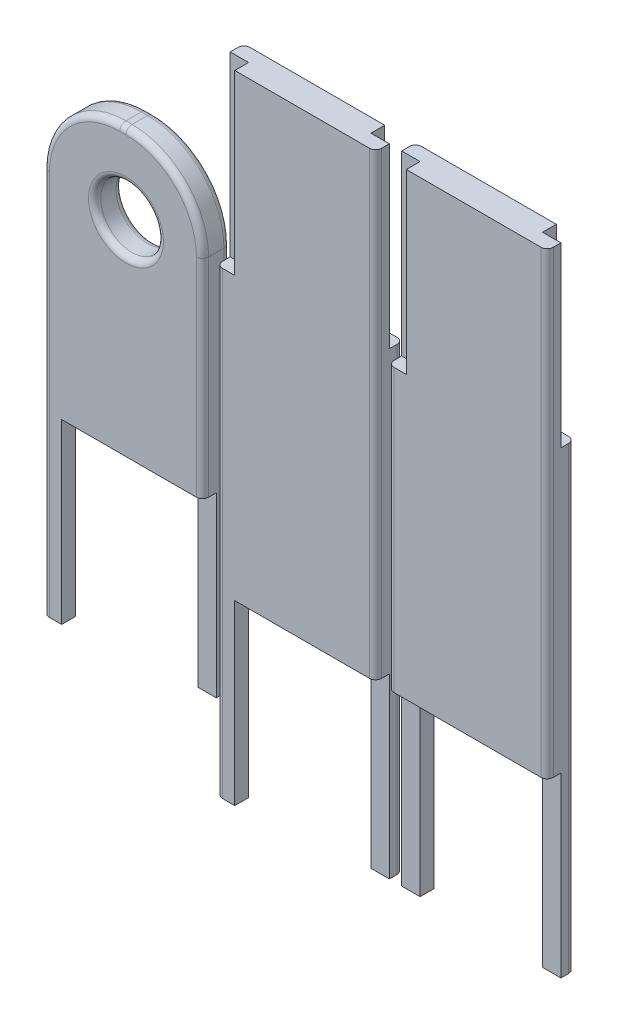
SolidWorks part; units mm, degrees
ref_plane "Front Plane" through (0, 0, 0) normal (0, 0, 1) x (1, 0, 0)
ref_plane "Top Plane" through (0, 0, 0) normal (0, 1, 0) x (1, 0, 0)
ref_plane "Right Plane" through (0, 0, 0) normal (1, 0, 0) x (0, 0, -1)
sketch "Sketch2" plane through (0, 0, 0) normal (0, 0, 1) x (1, 0, 0)
  line L1 (-127.5, 127.5) -> (127.5, 127.5) construction
  line L2 (-127.5, 127.5) -> (-127.5, -127.5) construction
  line L3 (-127.5, -127.5) -> (127.5, -127.5) construction
  line L4 (127.5, 127.5) -> (127.5, -127.5) construction
  line L5 (-127.5, 127.5) -> (127.5, -127.5) construction
  line L6 (-127.5, -127.5) -> (127.5, 127.5) construction
  line L15 (-80.9802, 72.2032) -> (-28.9802, 72.2032)
  line L16 (-80.9802, 72.2032) -> (-80.9802, -77.7968)
  line L17 (-80.9802, -77.7968) -> (-28.9802, -77.7968)
  line L18 (-28.9802, 72.2032) -> (-28.9802, -77.7968)
  line L19 (-80.9802, 72.2032) -> (-28.9802, -77.7968) construction
  line L20 (-80.9802, -77.7968) -> (-28.9802, 72.2032) construction
  point P0 (0, 0)
  point P6 (-54.9802, -2.7968)
  point P11 (-54.9802, -2.7968)
  dimension "D1" = 255
  dimension "D2" = 255
  dimension "D3" = 52
  dimension "D4" = 150
extrude "Boss-Extrude1" add sketch "Sketch2" along normal blind 9
sketch "Sketch3" plane through (0, 0, 0) normal (0, 0, 1) x (1, 0, 0)
  line L0 (-28.9802, 72.2032) -> (-80.9802, 72.2032) construction
  line L1 (-24.9263, 72.2032) -> (27.0737, 72.2032)
  line L2 (-24.9263, 72.2032) -> (-24.9263, -77.7968)
  line L3 (-24.9263, -77.7968) -> (27.0737, -77.7968)
  line L4 (27.0737, 72.2032) -> (27.0737, -77.7968)
  line L5 (-24.9263, 72.2032) -> (27.0737, -77.7968) construction
  line L6 (-24.9263, -77.7968) -> (27.0737, 72.2032) construction
  point P0 (1.0737, -2.7968)
  dimension "D1" = 52
  dimension "D2" = 150
extrude "Boss-Extrude2" add sketch "Sketch3" along normal blind 9 separate body
sketch "Sketch4" plane through (0, 0, 9) normal (0, 0, 1) x (1, 0, 0)
  line L1 (-24.9263, -77.7968) -> (-18.9263, -77.7968)
  line L2 (-24.9263, -77.7968) -> (-24.9263, -135.7968)
  line L3 (-24.9263, -135.7968) -> (-18.9263, -135.7968)
  line L4 (-18.9263, -77.7968) -> (-18.9263, -135.7968)
  line L5 (27.0737, -77.7968) -> (21.0737, -77.7968)
  line L6 (27.0737, -77.7968) -> (27.0737, -135.7968)
  line L7 (27.0737, -135.7968) -> (21.0737, -135.7968)
  line L8 (21.0737, -77.7968) -> (21.0737, -135.7968)
  dimension "D1" = 58
  dimension "D2" = 58
  dimension "D3" = 6
  dimension "D4" = 6
sketch "Sketch5" plane through (0, 0, 0) normal (0, 0, -1) x (-1, 0, 0)
  line L1 (24.9263, -135.7968) -> (18.9263, -135.7968) construction
  line L3 (24.9263, -77.7968) -> (24.9263, -135.7968) construction
  line L4 (18.9263, -77.7968) -> (18.9263, -135.7968) construction
  line L5 (24.9263, -77.7968) -> (18.9263, -77.7968) construction
  line L6 (-27.0737, -77.7968) -> (-21.0737, -77.7968) construction
  line L7 (-27.0737, -77.7968) -> (-27.0737, -135.7968) construction
  line L8 (-27.0737, -135.7968) -> (-21.0737, -135.7968) construction
  line L9 (-21.0737, -77.7968) -> (-21.0737, -135.7968) construction
  line L10 (24.9263, -135.7968) -> (18.9263, -135.7968)
  line L11 (24.9263, -77.7968) -> (24.9263, -135.7968)
  line L12 (18.9263, -77.7968) -> (18.9263, -135.7968)
  line L13 (24.9263, -77.7968) -> (18.9263, -77.7968)
  line L14 (-27.0737, -77.7968) -> (-21.0737, -77.7968)
  line L15 (-27.0737, -77.7968) -> (-27.0737, -135.7968)
  line L16 (-27.0737, -135.7968) -> (-21.0737, -135.7968)
  line L17 (-21.0737, -77.7968) -> (-21.0737, -135.7968)
extrude "Boss-Extrude3" add sketch "Sketch5" against normal blind 4.5
sketch "Sketch7" plane through (0, 0, 0) normal (0, 0, -1) x (-1, 0, 0)
  line L1 (-27.0737, 72.2032) -> (-21.0737, 72.2032)
  line L2 (-27.0737, 72.2032) -> (-27.0737, 14.2032)
  line L3 (-27.0737, 14.2032) -> (-21.0737, 14.2032)
  line L4 (-21.0737, 72.2032) -> (-21.0737, 14.2032)
  dimension "D1" = 58
  dimension "D2" = 6
extrude "Cut-Extrude1" cut sketch "Sketch7" against normal blind 4.5
sketch "Sketch8" plane through (0, 0, 9) normal (0, 0, 1) x (1, 0, 0)
  line L1 (-24.9263, 72.2032) -> (-18.9263, 72.2032)
  line L2 (-24.9263, 72.2032) -> (-24.9263, 14.2032)
  line L3 (-24.9263, 14.2032) -> (-18.9263, 14.2032)
  line L4 (-18.9263, 72.2032) -> (-18.9263, 14.2032)
  dimension "D1" = 58
  dimension "D2" = 6
extrude "Cut-Extrude2" cut sketch "Sketch8" against normal blind 4.5
sketch "Sketch9" plane through (0, 0, 0) normal (0, 0, -1) x (-1, 0, 0)
  line L1 (28.9802, -77.7968) -> (34.9802, -77.7968)
  line L2 (28.9802, -77.7968) -> (28.9802, -135.7968)
  line L3 (28.9802, -135.7968) -> (34.9802, -135.7968)
  line L4 (34.9802, -77.7968) -> (34.9802, -135.7968)
  dimension "D1" = 58
  dimension "D2" = 6
extrude "Boss-Extrude4" add sketch "Sketch9" against normal blind 4.5
sketch "Sketch10" plane through (0, 0, 9) normal (0, 0, 1) x (1, 0, 0)
  line L1 (-80.9802, -77.7968) -> (-74.9802, -77.7968)
  line L2 (-80.9802, -77.7968) -> (-80.9802, -135.7968)
  line L3 (-80.9802, -135.7968) -> (-74.9802, -135.7968)
  line L4 (-74.9802, -77.7968) -> (-74.9802, -135.7968)
  dimension "D1" = 58
  dimension "D2" = 6
extrude "Boss-Extrude5" add sketch "Sketch10" against normal blind 4.5
sketch "Sketch11" plane through (0, 0, 9) normal (0, 0, 1) x (1, 0, 0)
  line L0 (-80.9802, 124.2032) -> (-28.9802, 72.2032) construction
  line L1 (-80.9802, 72.2032) -> (-28.9802, 72.2032)
  line L2 (-80.9802, 72.2032) -> (-80.9802, 99.2032)
  line L3 (-55.9802, 124.2032) -> (-53.9802, 124.2032)
  line L4 (-28.9802, 72.2032) -> (-28.9802, 99.2032)
  line L5 (-28.9802, 124.2032) -> (-80.9802, 72.2032) construction
  arc A0 (-53.9802, 124.2032) -> (-28.9802, 99.2032) centre (-53.9802, 99.2032) cw
  arc A1 (-80.9802, 99.2032) -> (-55.9802, 124.2032) centre (-55.9802, 99.2032) cw
  point P8 (-28.9802, 124.2032)
  dimension "D3" = 25
  dimension "D1" = 52
  dimension "D2" = 52
sketch "Sketch12" plane through (0, 0, 0) normal (0, 0, 1) x (1, 0, 0)
  line L1 (-110.5185, 38.172) -> (-112.5185, 38.172)
  line L2 (-85.5185, 13.172) -> (-85.5185, -54.828)
  line L3 (-85.5185, -54.828) -> (-137.5185, -54.828)
  line L4 (-137.5185, 13.172) -> (-137.5185, -54.828)
  arc A0 (-110.5185, 38.172) -> (-85.5185, 13.172) centre (-110.5185, 13.172) cw
  arc A1 (-112.5185, 38.172) -> (-137.5185, 13.172) centre (-112.5185, 13.172) ccw
  point P6 (-85.5185, 38.172)
  point P9 (-137.5185, 38.172)
  dimension "D3" = 25
  dimension "D1" = 52
  dimension "D2" = 93
extrude "Boss-Extrude8" add sketch "Sketch12" along normal blind 9 separate body contours A0 L2 L3 L4 A1 L1
sketch "Sketch13" plane through (0, 0, 0) normal (0, 0, -1) x (-1, 0, 0)
  line L1 (28.9802, 72.2032) -> (34.9802, 72.2032)
  line L2 (28.9802, 72.2032) -> (28.9802, 14.2032)
  line L3 (28.9802, 14.2032) -> (34.9802, 14.2032)
  line L4 (34.9802, 72.2032) -> (34.9802, 14.2032)
  dimension "D1" = 58
  dimension "D2" = 6
extrude "Cut-Extrude3" cut sketch "Sketch13" against normal blind 4.5
sketch "Sketch14" plane through (0, 0, 9) normal (0, 0, 1) x (1, 0, 0)
  line L1 (-80.9802, 72.2032) -> (-74.9802, 72.2032)
  line L2 (-80.9802, 72.2032) -> (-80.9802, 14.2032)
  line L3 (-80.9802, 14.2032) -> (-74.9802, 14.2032)
  line L4 (-74.9802, 72.2032) -> (-74.9802, 14.2032)
  dimension "D1" = 58
  dimension "D2" = 6
extrude "Cut-Extrude4" cut sketch "Sketch14" against normal blind 4.5
sketch "Sketch15" plane through (0, 0, 9) normal (0, 0, 1) x (1, 0, 0)
  line L1 (-137.5185, -54.828) -> (-131.5185, -54.828)
  line L2 (-137.5185, -54.828) -> (-137.5185, -112.828)
  line L3 (-137.5185, -112.828) -> (-131.5185, -112.828)
  line L4 (-131.5185, -54.828) -> (-131.5185, -112.828)
  dimension "D1" = 58
  dimension "D2" = 6
extrude "Boss-Extrude9" add sketch "Sketch15" against normal blind 4.5
sketch "Sketch16" plane through (0, 0, 0) normal (0, 0, -1) x (-1, 0, 0)
  line L1 (85.5185, -54.828) -> (91.5185, -54.828)
  line L2 (85.5185, -54.828) -> (85.5185, -112.828)
  line L3 (85.5185, -112.828) -> (91.5185, -112.828)
  line L4 (91.5185, -54.828) -> (91.5185, -112.828)
  dimension "D1" = 58
  dimension "D2" = 6
extrude "Boss-Extrude10" add sketch "Sketch16" against normal blind 4.5
sketch "Sketch17" plane through (0, 0, 9) normal (0, 0, 1) x (1, 0, 0)
  line L0 (-137.5185, 13.172) -> (-137.5185, -112.828) construction
  line L1 (-137.5185, -13.828) -> (-110.5185, -13.828) construction
  line L2 (-137.5185, -13.828) -> (-137.5185, 38.172) construction
  line L3 (-137.5185, 38.172) -> (-110.5185, 38.172) construction
  line L4 (-110.5185, -13.828) -> (-110.5185, 38.172) construction
  line L5 (-110.5185, 12.172) -> (-137.5185, 12.172) construction
  circle A0 centre (-110.5185, 12.172) radius 10.25
  dimension "D2" = 20.5
  dimension "D1" = 52
extrude "Cut-Extrude5" cut sketch "Sketch17" against normal blind 13.5
fillet "Fillet1" radius 2 12 edges at (-137.5185, -20.828, 0) (-130.1962, 30.8497, 0) (-111.5185, 38.172, 0) (-92.8409, 30.8497, 0) (-85.5185, -20.828, 9) (-92.8409, 30.8497, 9) (-111.5185, 38.172, 9) (-137.5185, -49.828, 9) (-85.5185, -49.828, 0) (-130.1962, 30.8497, 9) (-100.2685, 12.172, 0) (-100.2685, 12.172, 9)
fillet "Fillet2" radius 2 4 edges at (-28.9802, -2.7968, 9) (-80.9802, -2.7968, 0) (-28.9802, -60.7968, 0) (-80.9802, -60.7968, 9)
fillet "Fillet3" radius 2 4 edges at (-24.9263, -31.7968, 0) (27.0737, -60.7968, 0) (-24.9263, -31.7968, 9) (27.0737, -2.7968, 9)
